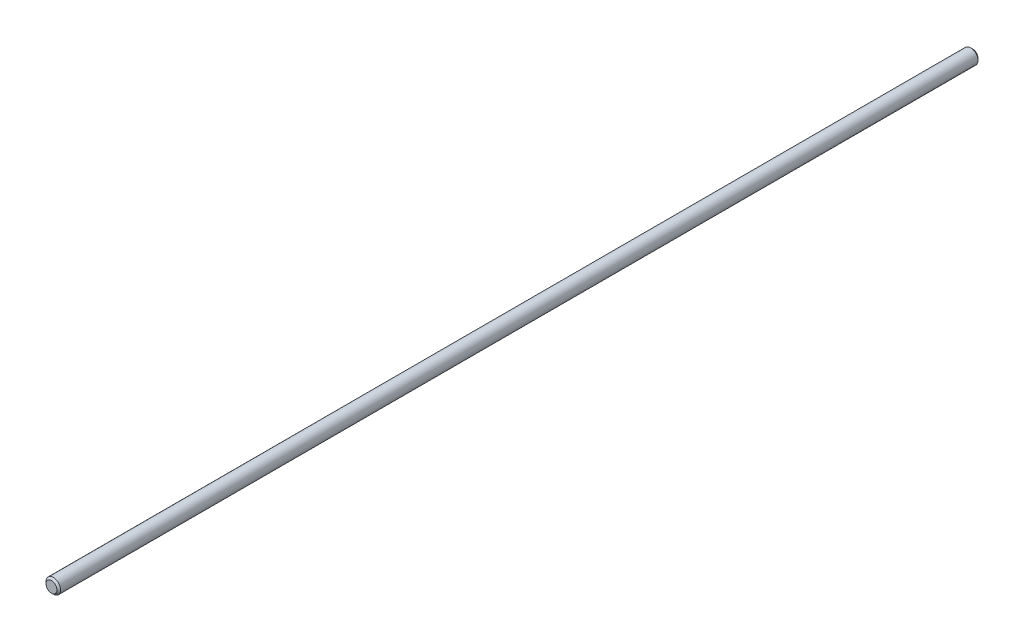
SolidWorks part; units mm, degrees
ref_plane "前视基准面" through (0, 0, 0) normal (0, 0, 1) x (1, 0, 0)
ref_plane "上视基准面" through (0, 0, 0) normal (0, 1, 0) x (1, 0, 0)
ref_plane "右视基准面" through (0, 0, 0) normal (1, 0, 0) x (0, 0, -1)
sketch "草图1" plane through (0, 0, 0) normal (0, 0, 1) x (1, 0, 0)
  circle A0 centre (0, 0) radius 4
  dimension "D1" = 8
extrude "凸台-拉伸1" add sketch "草图1" along normal blind 505
cosmetic thread "装饰螺纹线1" parameters "D1"=5, "D2"=6.647
chamfer "倒角1" distance 1 angle 45 2 edges at (4, 0, 0) (4, 0, 505)
